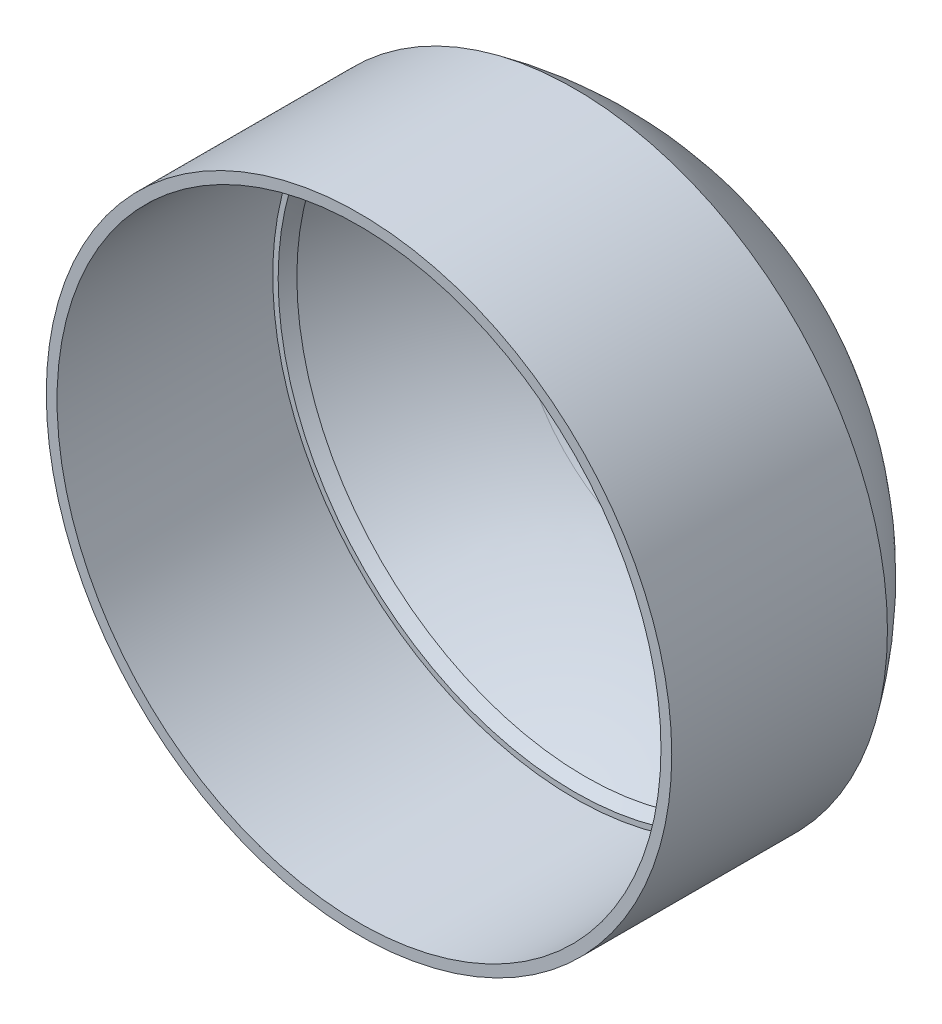
SolidWorks part; units mm, degrees
ref_plane "Front Plane" through (0, 0, 0) normal (0, 0, 1) x (1, 0, 0)
ref_plane "Top Plane" through (0, 0, 0) normal (0, 1, 0) x (1, 0, 0)
ref_plane "Right Plane" through (0, 0, 0) normal (1, 0, 0) x (0, 0, -1)
sketch "Sketch1" plane through (0, 0, 0) normal (0, 0, 1) x (1, 0, 0)
  circle A0 centre (0, 0) radius 28
  dimension "D1" = 56
extrude "Extrude-Thin1" add sketch "Sketch1" along normal mid plane 20 thin
sketch "Sketch5" plane through (0, 0, 0) normal (1, 0, 0) x (0, 0, -1)
  line L0 (10, 29) -> (10, 0)
  line L1 (10, -29) -> (10, 29) construction
  line L3 (0, 0) -> (10, 0) construction
  line L4 (10, 0) -> (25, 0)
  line L5 (10, 0) -> (25, 0) construction
  arc A0 (10, 29) -> (25, 0) centre (-9.9989, 0.2764) cw
  dimension "D1" = 35
  dimension "D2" = 25
revolve "Revolve-Thin4" add sketch "Sketch5" angle 360 about L3 wall 1
sketch "Sketch6" plane through (0, 0, -10) normal (0, 0, 1) x (1, 0, 0)
  circle A0 centre (0, 0) radius 1.5
  dimension "D1" = 3
sketch "Sketch7" plane through (0, 0, 0) normal (1, 0, 0) x (0, 0, -1)
  line L0 (10, 0) -> (24, 0)
  line L1 (10, 29) -> (10, -29) construction
  line L2 (10, 0) -> (10, 27.4968)
  arc A0 (10, 27.4968) -> (24, 0) centre (-8.996, 0.5125) cw
  dimension "D1" = 33
  dimension "D2" = 27.4968
  dimension "D3" = 24
revolve "Cut-Revolve1" cut sketch "Sketch7" angle 360 about L0
sketch "Sketch16" plane through (0, 0, 0) normal (0, 0, 1) x (1, 0, 0)
  circle A0 centre (0, 0) radius 1.5
  dimension "D1" = 3
extrude "Cut-Extrude2" cut sketch "Sketch16" against normal through all
extrude "Cut-Extrude1" cut sketch "Sketch6" against normal blind 1
